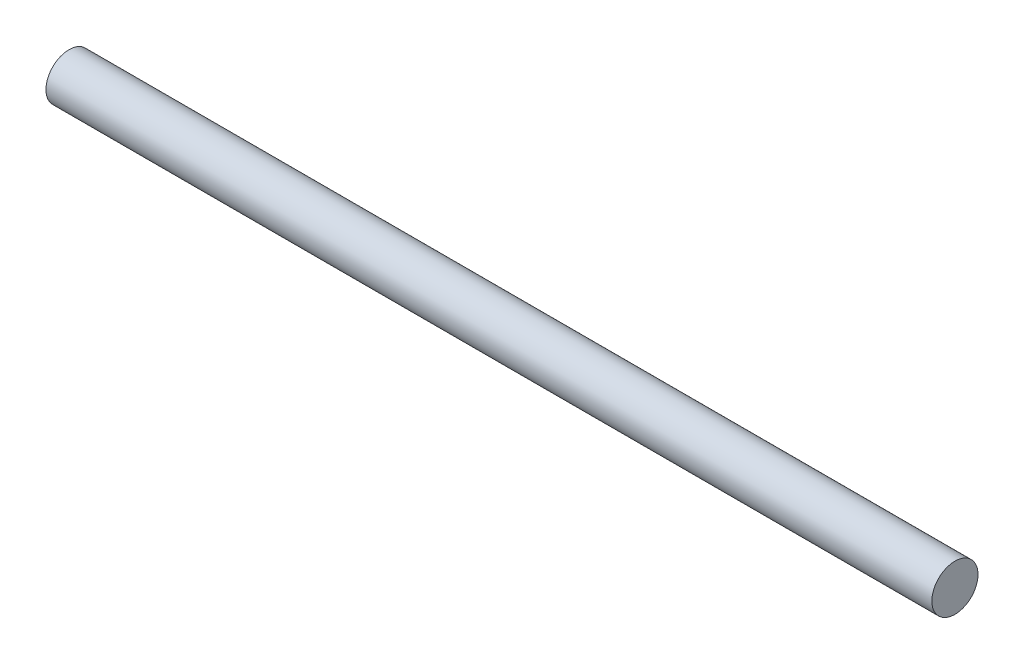
SolidWorks part; units mm, degrees
material "1023 Carbon Steel Sheet (SS)"
ref_plane "Front Plane" through (0, 0, 0) normal (0, 0, 1) x (1, 0, 0)
ref_plane "Top Plane" through (0, 0, 0) normal (0, 1, 0) x (1, 0, 0)
ref_plane "Right Plane" through (0, 0, 0) normal (1, 0, 0) x (0, 0, -1)
sketch "Sketch1" plane through (0, 0, 0) normal (1, 0, 0) x (0, 0, -1)
  circle A0 centre (0, 0) radius 2.5
  point P3 (0, 0)
  point P4 (0, 0)
extrude "Boss-Extrude1" add sketch "Sketch1" along normal blind 96
